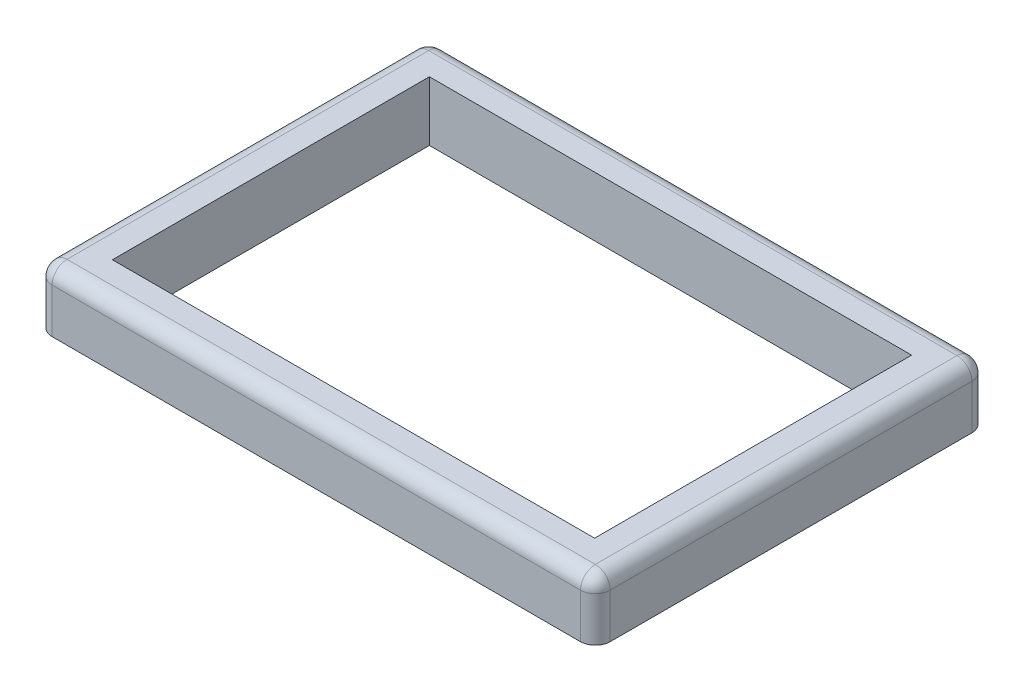
SolidWorks part; units mm, degrees
ref_plane "Front Plane" through (0, 0, 0) normal (0, 0, 1) x (1, 0, 0)
ref_plane "Top Plane" through (0, 0, 0) normal (0, 1, 0) x (1, 0, 0)
ref_plane "Right Plane" through (0, 0, 0) normal (1, 0, 0) x (0, 0, -1)
sketch "Sketch2" plane through (0, 0, 0) normal (0, 1, 0) x (1, 0, 0)
  line L1 (-47.625, 33.401) -> (47.625, 33.401)
  line L2 (-47.625, 33.401) -> (-47.625, -33.401)
  line L3 (-47.625, -33.401) -> (47.625, -33.401)
  line L4 (47.625, 33.401) -> (47.625, -33.401)
  line L5 (-47.625, 33.401) -> (47.625, -33.401) construction
  line L6 (-47.625, -33.401) -> (47.625, 33.401) construction
  line L7 (-41.148, 27.051) -> (41.148, 27.051)
  line L8 (-41.148, 27.051) -> (-41.148, -27.051)
  line L9 (-41.148, -27.051) -> (41.148, -27.051)
  line L10 (41.148, 27.051) -> (41.148, -27.051)
  line L11 (-41.148, 27.051) -> (41.148, -27.051) construction
  line L12 (-41.148, -27.051) -> (41.148, 27.051) construction
  point P0 (0, 0)
  point P6 (0, 0)
  point P11 (0, 27.051)
  dimension "D1" = 95.25
  dimension "D2" = 66.802
  dimension "D3" = 54.102
  dimension "D4" = 82.296
extrude "Boss-Extrude1" add sketch "Sketch2" along normal blind 10.16 contours L10 L7 L8 L9 | L1 L4 L3 L2
sketch "Sketch3" plane through (0, 0, 0) normal (0, -1, 0) x (1, 0, 0)
  line L4 (-44.45, 30.48) -> (44.45, 30.48)
  line L5 (-44.45, 30.48) -> (-44.45, -30.48)
  line L6 (-44.45, -30.48) -> (44.45, -30.48)
  line L7 (44.45, 30.48) -> (44.45, -30.48)
  line L8 (-44.45, 30.48) -> (44.45, -30.48) construction
  line L9 (-44.45, -30.48) -> (44.45, 30.48) construction
  circle A4 centre (-44.45, 30.48) radius 1.9939
  circle A5 centre (44.45, 30.48) radius 1.9939
  circle A6 centre (44.45, -30.48) radius 1.8669
  circle A7 centre (-44.45, -30.48) radius 1.9939
  point P0 (0, 0)
  dimension "D3" = 3.9878
  dimension "D4" = 3.9878
  dimension "D5" = 3.7338
  dimension "D6" = 3.9878
  dimension "D1" = 88.9
  dimension "D2" = 60.96
extrude "Cut-Extrude1" cut sketch "Sketch3" against normal blind 7.62 contours A4 | A7 | A6 | A5
sketch "Sketch4" plane through (0, 0, 27.051) normal (0, 0, -1) x (-1, 0, 0)
  line L0 (47.625, 0) -> (-47.625, 0) construction
  line L1 (-30.353, 0) -> (-24.003, 0)
  line L2 (-30.353, 0) -> (-30.353, 6.2484)
  line L3 (-30.353, 6.2484) -> (-24.003, 6.2484)
  line L4 (-24.003, 0) -> (-24.003, 6.2484)
  line L5 (0, 0) -> (0, 10.16) construction
  line L6 (41.148, 0) -> (-41.148, 0) construction
  line L7 (41.148, 10.16) -> (-41.148, 10.16) construction
  line L8 (30.353, 6.2484) -> (24.003, 6.2484)
  line L9 (24.003, 0) -> (24.003, 6.2484)
  line L10 (30.353, 0) -> (24.003, 0)
  line L11 (30.353, 0) -> (30.353, 6.2484)
  point P6 (-27.178, 0)
  line M6 (-41.148, 0) -> (41.148, 0)
  dimension "D1" = 13.97
  dimension "D2" = 6.35
  dimension "D3" = 6.2484
extrude "Cut-Extrude2" cut sketch "Sketch4" against normal blind 2.54 contours L11 L8 L9 M6 | L2 L3 L4 L1
sketch "Sketch6" plane through (41.148, 0, 0) normal (-1, 0, 0) x (0, 0, 1)
  line L0 (-33.401, 0) -> (33.401, 0) construction
  line L1 (-27.051, 0) -> (-19.431, 0)
  line L2 (-27.051, 0) -> (-27.051, 6.2484)
  line L3 (-27.051, 6.2484) -> (-19.431, 6.2484)
  line L4 (-19.431, 0) -> (-19.431, 6.2484)
  line L5 (-27.051, 10.16) -> (-27.051, 0) construction
  line L6 (0, 0) -> (0, 10.16) construction
  line L7 (-27.051, 0) -> (27.051, 0) construction
  line L8 (-27.051, 10.16) -> (27.051, 10.16) construction
  line L9 (27.051, 6.2484) -> (19.431, 6.2484)
  line L10 (19.431, 0) -> (19.431, 6.2484)
  line L11 (27.051, 0) -> (19.431, 0)
  line L12 (27.051, 0) -> (27.051, 6.2484)
  line L14 (-3.175, 0) -> (3.175, 0)
  line L15 (-3.175, 0) -> (-3.175, 6.2484)
  line L16 (-3.175, 6.2484) -> (3.175, 6.2484)
  line L17 (3.175, 0) -> (3.175, 6.2484)
  point P22 (0, 0)
  dimension "D1" = 7.62
  dimension "D2" = 6.2484
  dimension "D3" = 6.35
  dimension "D4" = 6.2484
extrude "Cut-Extrude3" cut sketch "Sketch6" against normal blind 2.54
fillet "Fillet1" radius 2.54 8 edges at (47.625, 5.08, -33.401) (-47.625, 5.08, -33.401) (-47.625, 5.08, 33.401) (47.625, 5.08, 33.401) (47.625, 10.16, 0) (0, 10.16, -33.401) (-47.625, 10.16, 0) (0, 10.16, 33.401)
